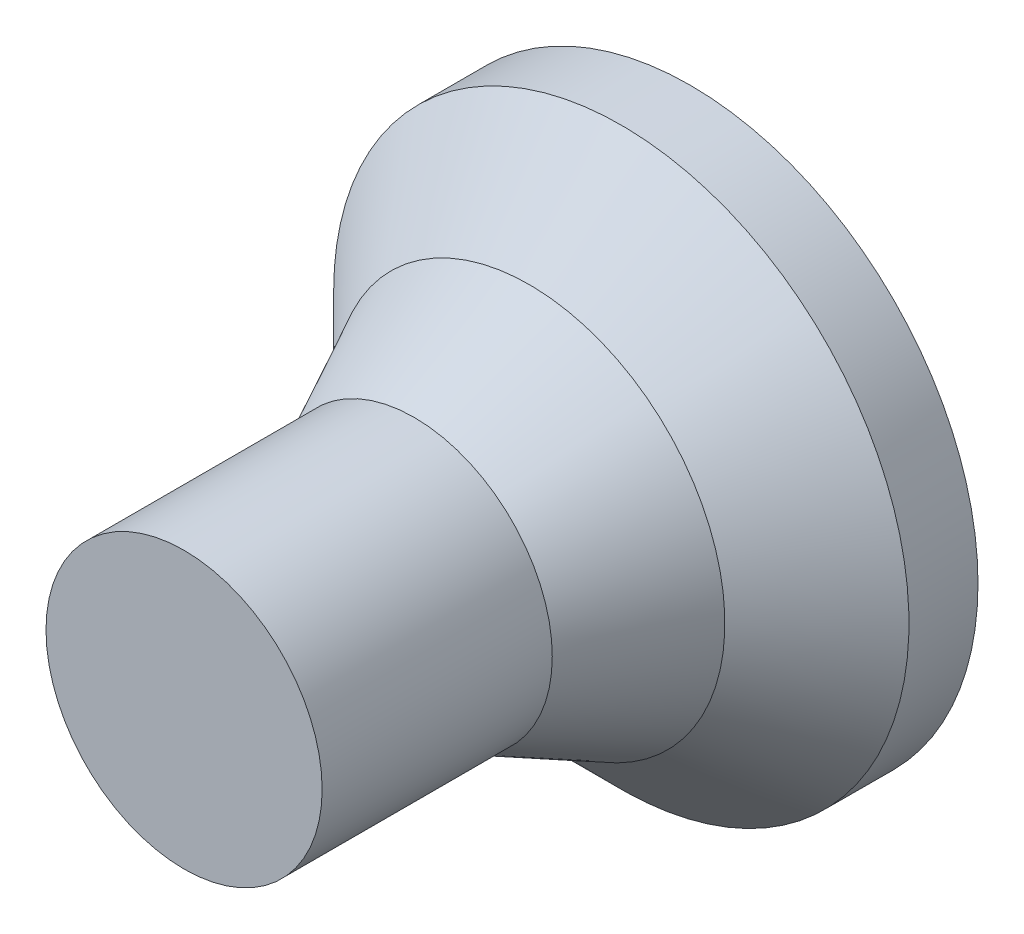
SolidWorks part; units mm, degrees
ref_plane "正面" through (0, 0, 0) normal (0, 0, 1) x (1, 0, 0)
ref_plane "平面" through (0, 0, 0) normal (0, 1, 0) x (1, 0, 0)
ref_plane "右側面" through (0, 0, 0) normal (1, 0, 0) x (0, 0, -1)
sketch "ｽｹｯﾁ1" plane through (0, 0, 0) normal (0, 0, 1) x (1, 0, 0)
  circle A0 centre (0, 0) radius 125
  dimension "D1" = 250
extrude "ﾎﾞｽ - 押し出し1" add sketch "ｽｹｯﾁ1" along normal blind 30
ref_plane "平面1" through (0, 0, 70) normal (0, 0, -1) x (-1, 0, 0)
sketch "ｽｹｯﾁ3" plane through (0, 0, 70) normal (0, 0, -1) x (-1, 0, 0)
  circle A0 centre (0, 0) radius 85
  dimension "D1" = 170
ref_plane "平面2" through (0, 0, 120) normal (0, 0, -1) x (-1, 0, 0)
sketch "ｽｹｯﾁ4" plane through (0, 0, 120) normal (0, 0, -1) x (-1, 0, 0)
  circle A0 centre (0, 0) radius 60
  dimension "D1" = 120
extrude "ﾎﾞｽ - 押し出し2" add sketch "ｽｹｯﾁ4" against normal blind 100 separate body
loft "ﾛﾌﾄ1" add profiles "ｽｹｯﾁ3" section "ｽｹｯﾁ3" section edge at (125, 0, 30)
loft "ﾛﾌﾄ2" add section face at (-85, 0, 70) section face at (-60, 0, 120)
